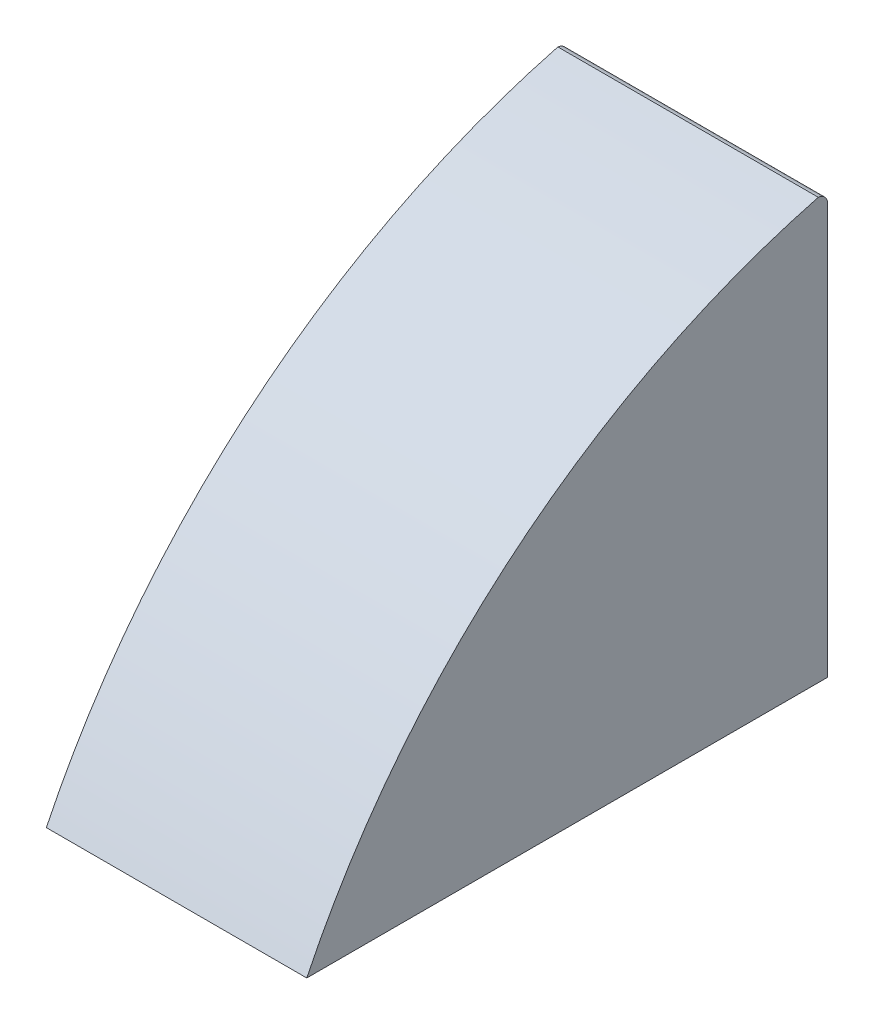
SolidWorks part; units mm, degrees
ref_plane "Front Plane" through (0, 0, 0) normal (0, 0, 1) x (1, 0, 0)
ref_plane "Top Plane" through (0, 0, 0) normal (0, 1, 0) x (1, 0, 0)
ref_plane "Right Plane" through (0, 0, 0) normal (1, 0, 0) x (0, 0, -1)
sketch "Sketch1" plane through (0, 0, 0) normal (1, 0, 0) x (0, 0, -1)
  line L0 (-17.1359, 4.9409) -> (-4.4359, 4.9409)
  line L1 (-4.4359, 4.9409) -> (-4.4359, 14.9409)
  arc A2 (-4.4359, 14.9409) -> (-4.6639, 15.1899) centre (-4.6859, 14.9409) ccw
  arc A3 (-17.1359, 4.9409) -> (-4.6639, 15.1899) centre (0.1897, -3.4295) cw
  point P2 (0, 0)
  dimension "D1" = 10
  dimension "D4" = 0.25
  dimension "D2" = 12.7
extrude "Boss-Extrude1" add sketch "Sketch1" along normal blind 6.35
